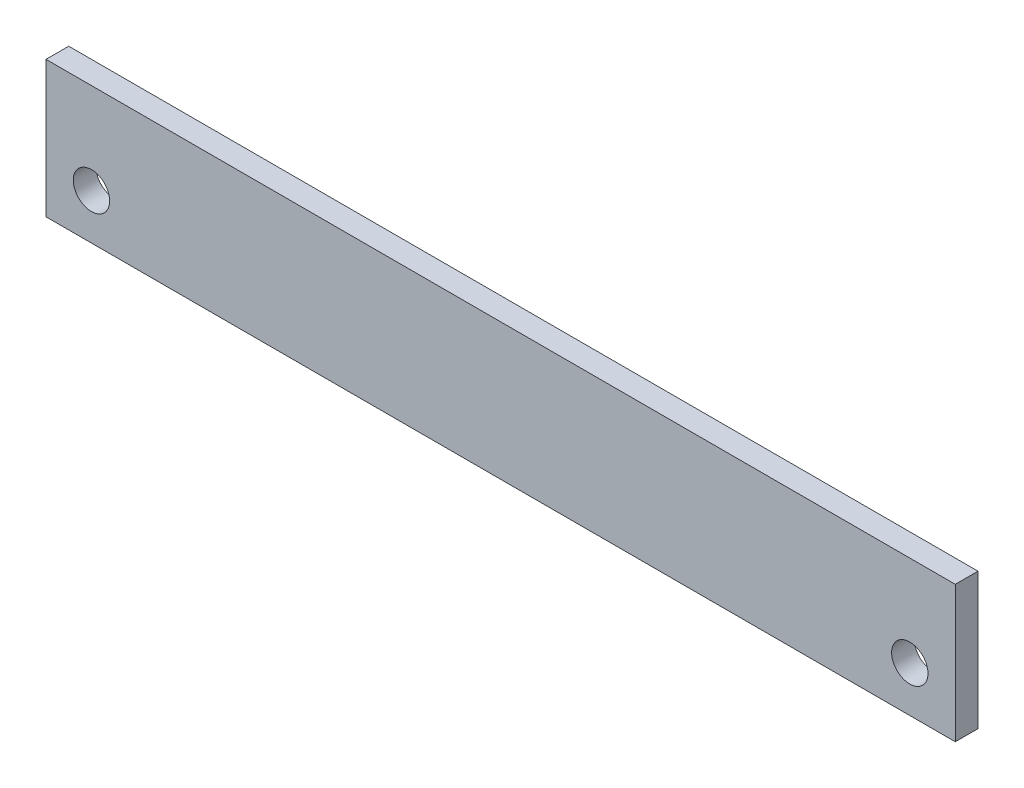
SolidWorks part; units mm, degrees
ref_plane "Front Plane" through (0, 0, 0) normal (0, 0, 1) x (1, 0, 0)
ref_plane "Top Plane" through (0, 0, 0) normal (0, 1, 0) x (1, 0, 0)
ref_plane "Right Plane" through (0, 0, 0) normal (1, 0, 0) x (0, 0, -1)
sketch "Sketch1" plane through (0, 0, 0) normal (0, 0, 1) x (1, 0, 0)
  line L1 (-100, -15) -> (100, -15)
  line L2 (-100, -15) -> (-100, 15)
  line L3 (-100, 15) -> (100, 15)
  line L4 (100, -15) -> (100, 15)
  line L5 (-100, -15) -> (100, 15) construction
  line L6 (-100, 15) -> (100, -15) construction
  point P0 (0, 0)
  dimension "D1" = 30
  dimension "D2" = 200
extrude "Boss-Extrude1" add sketch "Sketch1" along normal blind 5
sketch "Sketch2" plane through (0, 0, 5) normal (0, 0, 1) x (1, 0, 0)
  line L0 (-100, 15) -> (-100, -15) construction
  line L2 (100, 15) -> (-100, 15) construction
  circle A0 centre (-90, -5) radius 4
  circle A1 centre (90, -5) radius 4
  dimension "D1" = 8
  dimension "D2" = 10
  dimension "D3" = 20
extrude "Cut-Extrude1" cut sketch "Sketch2" against normal blind 5
